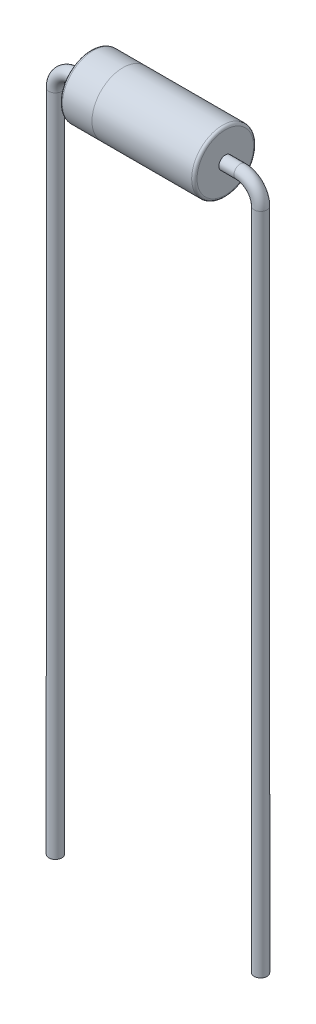
SolidWorks part; units mm, degrees
material "Plain Carbon Steel"
ref_plane "Front Plane" through (0, 0, 0) normal (0, 0, 1) x (1, 0, 0)
ref_plane "Top Plane" through (0, 0, 0) normal (0, 1, 0) x (1, 0, 0)
ref_plane "Right Plane" through (0, 0, 0) normal (1, 0, 0) x (0, 0, -1)
sketch "Sketch1" plane through (0, 0, 0) normal (0, 0, 1) x (1, 0, 0)
  line L0 (-3.06, 0) -> (3.06, 0)
  line L1 (-3.81, -0.75) -> (-3.81, -25.4)
  line L2 (3.81, -0.75) -> (3.81, -25.4)
  line L3 (-3.81, -25.4) -> (3.81, -25.4) construction
  line L4 (0, 0) -> (0, -25.4) construction
  arc A0 (-3.06, 0) -> (-3.81, -0.75) centre (-3.06, -0.75) ccw
  arc A1 (3.06, 0) -> (3.81, -0.75) centre (3.06, -0.75) cw
  dimension "D2" = 0.75
  dimension "D1" = 7.62
  dimension "D3" = 25.4
ref_plane "Plane1" through (-3.81, -25.4, 0) normal (0, -1, 0) x (-1, 0, 0)
sketch "Sketch2" plane through (-3.81, -25.4, 0) normal (0, -1, 0) x (-1, 0, 0)
  circle A0 centre (0, 0) radius 0.24
  dimension "D1" = 0.48
sweep "Sweep1" add profiles "Sketch2" path "Sketch1"
sketch "Sketch3" plane through (0, 0, 0) normal (0, 0, 1) x (1, 0, 0)
  line L0 (-1.3, 1.15) -> (-2.4, 1.15) construction
  line L1 (-1.3, 1.15) -> (2.4, 1.15)
  line L2 (-1.3, 1.15) -> (-1.3, 0)
  line L3 (-1.3, 0) -> (2.5, 0)
  line L4 (2.5, 1.05) -> (2.5, 0)
  line L5 (-2.5, 1.05) -> (-2.5, 0) construction
  line L6 (-3.06, 0) -> (3.06, 0) construction
  line L7 (-2.5, 0) -> (-1.3, 0) construction
  arc A0 (2.4, 1.15) -> (2.5, 1.05) centre (2.4, 1.05) cw
  arc A1 (-2.4, 1.15) -> (-2.5, 1.05) centre (-2.4, 1.05) ccw construction
  point P14 (2.5, 1.15)
  dimension "D5" = 0.1
  dimension "D6" = 0.1
  dimension "D1" = 2.5
  dimension "D2" = 3.8
  dimension "D3" = 1.15
  dimension "D4" = 2.5
revolve "Revolve1" add sketch "Sketch3" angle 360 about L3
sketch "Sketch4" plane through (0, 0, 0) normal (0, 0, 1) x (1, 0, 0)
  line L0 (-2.5, 1.05) -> (-2.5, 0) construction
  line L1 (-1.3, 1.15) -> (-2.4, 1.15) construction
  line L2 (-1.3, 1.15) -> (-1.3, 0) construction
  line L3 (-2.5, 0) -> (-1.3, 0) construction
  line L4 (-2.5, 1.05) -> (-2.5, 0)
  line L5 (-1.3, 1.15) -> (-2.4, 1.15)
  line L6 (-1.3, 1.15) -> (-1.3, 0)
  line L7 (-2.5, 0) -> (-1.3, 0)
  arc A0 (-2.4, 1.15) -> (-2.5, 1.05) centre (-2.4, 1.05) ccw construction
  arc A1 (-2.4, 1.15) -> (-2.5, 1.05) centre (-2.4, 1.05) ccw
revolve "Revolve2" add sketch "Sketch4" angle 360 about L7
